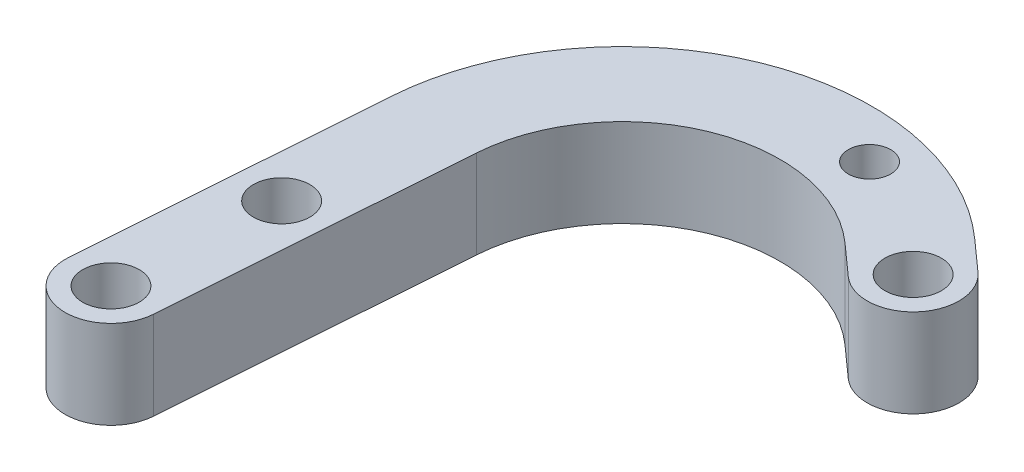
SolidWorks part; units mm, degrees
ref_plane "Płaszczyzna przednia" through (0, 0, 0) normal (0, 0, 1) x (1, 0, 0)
ref_plane "Płaszczyzna górna" through (0, 0, 0) normal (0, 1, 0) x (1, 0, 0)
ref_plane "Płaszczyzna prawa" through (0, 0, 0) normal (1, 0, 0) x (0, 0, -1)
sketch "Szkic1" plane through (0, 0, 0) normal (0, 1, 0) x (1, 0, 0)
  line L0 (-145.9217, -1.8275) -> (-139.7535, 83.4134)
  line L1 (-22.2612, 130.9857) -> (-13.5989, 123.2474)
  line L2 (-119.9895, -3.704) -> (-113.8213, 81.5369)
  line L3 (-39.5827, 111.5959) -> (-30.9204, 103.8576)
  circle A0 centre (-132.9556, -2.7657) radius 8
  arc A1 (-145.9217, -1.8275) -> (-119.9895, -3.704) centre (-132.9556, -2.7657) ccw
  arc A2 (-30.9204, 103.8576) -> (-13.5989, 123.2474) centre (-22.2597, 113.5525) ccw
  circle A3 centre (-22.2597, 113.5525) radius 8
  arc A4 (-22.2612, 130.9857) -> (-139.7535, 83.4134) centre (-69.3126, 78.3162) ccw
  arc A5 (-39.5827, 111.5959) -> (-113.8213, 81.5369) centre (-69.3126, 78.3162) ccw
  point P2 (-7.4387, 102.0953)
  point P4 (-22.2612, 113.5525)
  dimension "D1" = 26
  dimension "D2" = 70.6251
extrude "Dodanie-wyciągnięcie1" add sketch "Szkic1" along normal blind 25
sketch "Szkic2" plane through (0, 25, 0) normal (0, 1, 0) x (1, 0, 0)
  line L0 (-13.5989, 123.2474) -> (-22.2612, 130.9857) construction
  circle A0 centre (-56.0349, 134.9822) radius 6
  circle A2 centre (-22.2597, 113.5525) radius 8 construction
  dimension "D1" = 19.52
  dimension "D2" = 40
extrude "Wytnij-wyciągnięcie1" cut sketch "Szkic2" against normal up to surface (25 mm away) contours A0 up to face at (-80.1577, 0, -83.3964)
sketch "Szkic3" plane through (0, 25, 0) normal (0, 1, 0) x (1, 0, 0)
  circle A0 centre (-129.6549, 42.2343) radius 8
  circle A1 centre (-132.9556, -2.7657) radius 8 construction
  point P4 (-129.6549, 42.2343)
  dimension "D1" = 45
extrude "Wytnij-wyciągnięcie2" cut sketch "Szkic3" against normal blind 2000
